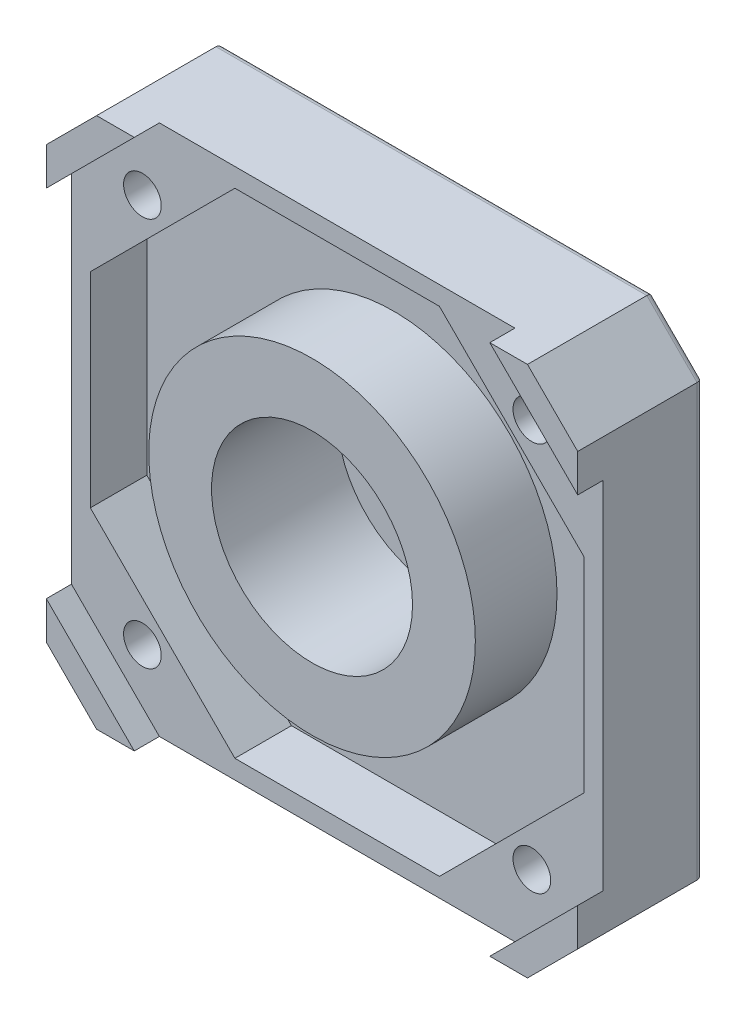
SolidWorks part; units mm, degrees
ref_plane "Front Plane" through (0, 0, 0) normal (0, 0, 1) x (1, 0, 0)
ref_plane "Top Plane" through (0, 0, 0) normal (0, 1, 0) x (1, 0, 0)
ref_plane "Right Plane" through (0, 0, 0) normal (1, 0, 0) x (0, 0, -1)
sketch "Sketch2" plane through (0, 0, 0) normal (0, 0, 1) x (1, 0, 0)
  line L0 (-21.15, 17.15) -> (-17.15, 21.15)
  line L1 (-17.15, -21.15) -> (17.15, -21.15)
  line L2 (-21.15, -17.15) -> (-21.15, 17.15)
  line L3 (-17.15, 21.15) -> (17.15, 21.15)
  line L4 (21.15, -17.15) -> (21.15, 17.15)
  line L5 (-21.15, -21.15) -> (21.15, 21.15) construction
  line L6 (-21.15, 21.15) -> (21.15, -21.15) construction
  line L7 (17.15, 21.15) -> (21.15, 17.15)
  line L8 (17.15, -21.15) -> (21.15, -17.15)
  line L9 (-21.15, -17.15) -> (-17.15, -21.15)
  point P0 (0, 0)
  dimension "D1" = 42.3
  dimension "D2" = 42.3
extrude "Boss-Extrude1" add sketch "Sketch2" along normal blind 10
sketch "Sketch17" plane through (0, 0, 0) normal (0, 0, -1) x (-1, 0, 0)
  circle A0 centre (0, 0) radius 11
  dimension "D1" = 22
extrude "Boss-Extrude4" add sketch "Sketch17" along normal blind 2
sketch "Sketch18" plane through (0, 0, 10) normal (0, 0, 1) x (1, 0, 0)
  line L0 (17.15, 21.15) -> (-17.15, 21.15) construction
  line L1 (8.1393, 19.65) -> (-8.1393, 19.65)
  line L2 (-8.1393, 19.65) -> (-19.65, 8.1393)
  line L3 (-19.65, 8.1393) -> (-19.65, -8.1393)
  line L4 (-19.65, -8.1393) -> (-8.1393, -19.65)
  line L5 (-8.1393, -19.65) -> (8.1393, -19.65)
  line L6 (8.1393, -19.65) -> (19.65, -8.1393)
  line L7 (19.65, -8.1393) -> (19.65, 8.1393)
  line L8 (19.65, 8.1393) -> (8.1393, 19.65)
  circle A0 centre (0, 0) radius 19.65 construction
  circle A1 centre (0, 0) radius 13
  dimension "D2" = 26
  dimension "D1" = 1.5
extrude "Cut-Extrude14" cut sketch "Sketch18" against normal blind 6.5
sketch "Sketch19" plane through (0, 0, 10) normal (0, 0, 1) x (1, 0, 0)
  circle A0 centre (0, 0) radius 8
  dimension "D1" = 16
extrude "Cut-Extrude15" cut sketch "Sketch19" against normal blind 10
sketch "Sketch20" plane through (0, 0, 0) normal (0, 0, 1) x (1, 0, 0)
  circle A0 centre (0, 0) radius 4.5
  dimension "D1" = 9
extrude "Cut-Extrude16" cut sketch "Sketch20" against normal through all
sketch "Sketch21" plane through (0, 0, 10) normal (0, 0, 1) x (1, 0, 0)
  line L0 (-21.15, 14.15) -> (-14.15, 21.15)
  line L1 (-14.15, -21.15) -> (14.15, -21.15)
  line L2 (-21.15, -14.15) -> (-21.15, 14.15)
  line L3 (-14.15, 21.15) -> (14.15, 21.15)
  line L4 (21.15, -14.15) -> (21.15, 14.15)
  line L5 (-21.15, -21.15) -> (21.15, 21.15) construction
  line L6 (-21.15, 21.15) -> (21.15, -21.15) construction
  line L7 (14.15, 21.15) -> (21.15, 14.15)
  line L8 (-21.15, -14.15) -> (-14.15, -21.15)
  line L9 (14.15, -21.15) -> (21.15, -14.15)
  circle A0 centre (0, 0) radius 13
  point P0 (0, 0)
  dimension "D3" = 26
  dimension "D1" = 42.3
  dimension "D2" = 42.3
extrude "Cut-Extrude17" cut sketch "Sketch21" against normal blind 2
sketch "Sketch23" plane through (0, 0, 10) normal (0, 0, 1) x (1, 0, 0)
  line L1 (-15.5, -15.5) -> (15.5, -15.5) construction
  line L2 (-15.5, -15.5) -> (-15.5, 15.5) construction
  line L3 (-15.5, 15.5) -> (15.5, 15.5) construction
  line L4 (15.5, -15.5) -> (15.5, 15.5) construction
  line L5 (-15.5, -15.5) -> (15.5, 15.5) construction
  line L6 (-15.5, 15.5) -> (15.5, -15.5) construction
  circle A0 centre (-15.5, 15.5) radius 1.5
  circle A1 centre (15.5, 15.5) radius 1.5
  circle A2 centre (15.5, -15.5) radius 1.5
  circle A3 centre (-15.5, -15.5) radius 1.5
  point P1 (0, 0)
  dimension "D2" = 3
  dimension "D1" = 31
extrude "Cut-Extrude18" cut sketch "Sketch23" against normal through all
sketch "Sketch24" plane through (0, 0, 0) normal (0, 0, -1) x (-1, 0, 0)
  circle A0 centre (0, 0) radius 16
  circle A1 centre (0, 0) radius 11
  dimension "D1" = 32
extrude "Cut-Extrude19" cut sketch "Sketch24" against normal blind 0.25
fillet "Fillet9" radius 0.5 11 edges at (4.5, 0, -2) (-11, 0, -2) (19.15, -19.15, 0) (0, -21.15, 0) (-19.15, -19.15, 0) (-21.15, 0, 0) (-19.15, 19.15, 0) (0, 21.15, 0) (19.15, 19.15, 0) (21.15, 0, 0) (-11, 0, 0.25)
chamfer "Chamfer1" distance 0.5 angle 45 4 edges at (-17, -15.5, 0) (14, -15.5, 0) (14, 15.5, 0) (-17, 15.5, 0)
